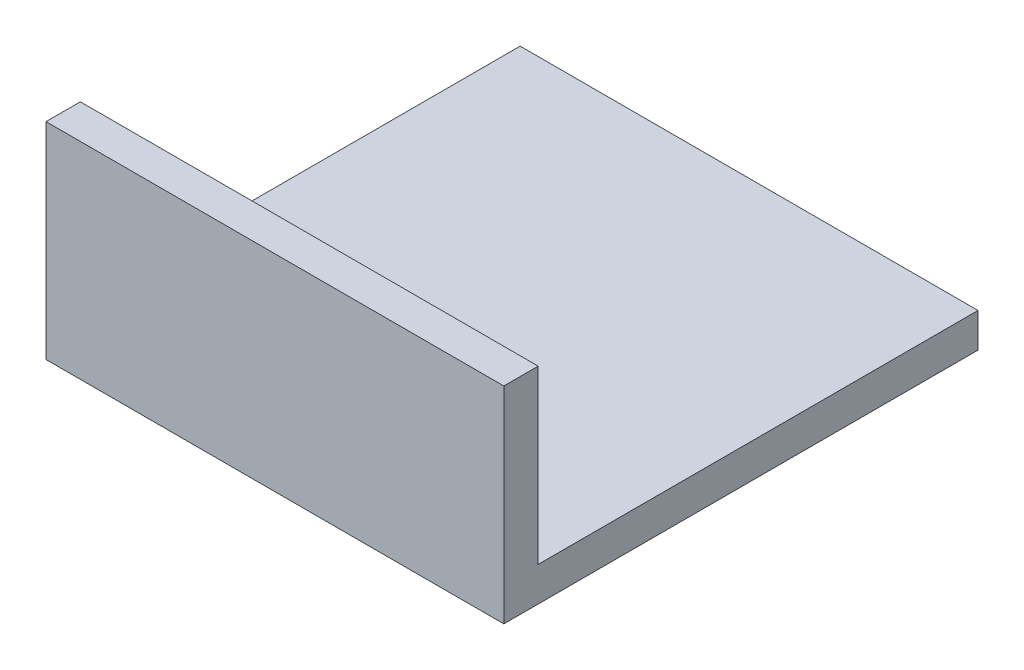
SolidWorks part; units mm, degrees
material "1060 Alloy"
ref_plane "Front Plane" through (0, 0, 0) normal (0, 0, 1) x (1, 0, 0)
ref_plane "Top Plane" through (0, 0, 0) normal (0, 1, 0) x (1, 0, 0)
ref_plane "Right Plane" through (0, 0, 0) normal (1, 0, 0) x (0, 0, -1)
sketch "Sketch1" plane through (0, 0, 0) normal (0, 0, 1) x (1, 0, 0)
  line L1 (0, 0) -> (127, 0)
  line L2 (0, 0) -> (0, 57.15)
  line L3 (0, 57.15) -> (127, 57.15)
  line L4 (127, 0) -> (127, 57.15)
extrude "Boss-Extrude1" add sketch "Sketch1" along normal blind 9.525
sketch "Sketch2" plane through (0, 0, 0) normal (0, 1, 0) x (1, 0, 0)
  line L0 (0, -9.525) -> (0, 0) construction
  line L1 (0, -5.0038) -> (127, -5.0038)
  line L2 (0, -5.0038) -> (0, 121.9962)
  line L3 (0, 121.9962) -> (127, 121.9962)
  line L4 (127, -5.0038) -> (127, 121.9962)
extrude "Boss-Extrude3" add sketch "Sketch2" along normal blind 9.525
sketch "Sketch3" plane through (0, 0, 0) normal (0, 1, 0) x (1, 0, 0)
  circle A0 centre (63.5, 36.322) radius 10.16
extrude "Cut-Extrude1" cut sketch "Sketch3" along normal blind 5.0038
